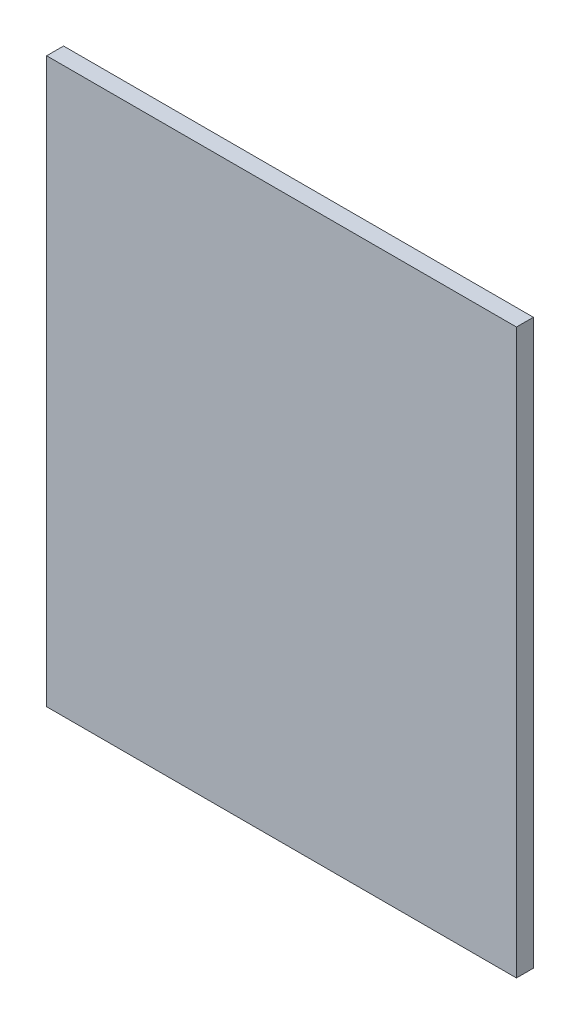
SolidWorks part; units mm, degrees
ref_plane "Front Plane" through (0, 0, 0) normal (0, 0, 1) x (1, 0, 0)
ref_plane "Top Plane" through (0, 0, 0) normal (0, 1, 0) x (1, 0, 0)
ref_plane "Right Plane" through (0, 0, 0) normal (1, 0, 0) x (0, 0, -1)
sketch "Sketch1" plane through (0, 0, 0) normal (0, 0, 1) x (1, 0, 0)
  line L1 (250, -300) -> (-250, -300)
  line L2 (250, -300) -> (250, 300)
  line L3 (250, 300) -> (-250, 300)
  line L4 (-250, -300) -> (-250, 300)
  line L5 (250, -300) -> (-250, 300) construction
  line L6 (250, 300) -> (-250, -300) construction
  point P0 (0, 0)
  dimension "D1" = 600
  dimension "D2" = 500
extrude "Boss-Extrude1" add sketch "Sketch1" along normal blind 18
equation "\"H_DSP\"=18"
equation "\"D1@Boss-Extrude1\"=\"H_DSP\""
